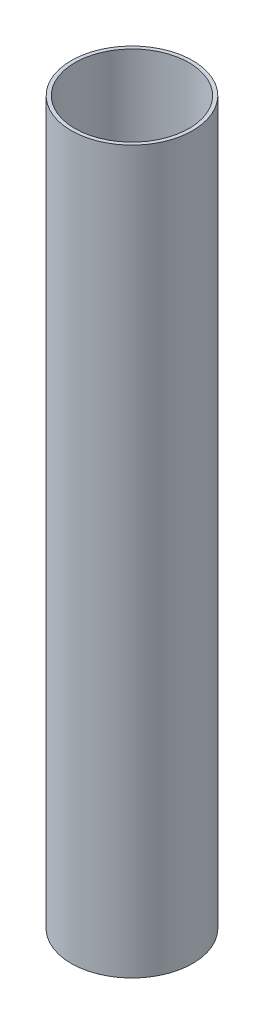
SolidWorks part; units mm, degrees
material "Alumina"
ref_plane "Front Plane" through (0, 0, 0) normal (0, 0, 1) x (1, 0, 0)
ref_plane "Top Plane" through (0, 0, 0) normal (0, 1, 0) x (1, 0, 0)
ref_plane "Right Plane" through (0, 0, 0) normal (1, 0, 0) x (0, 0, -1)
sketch "Sketch1" plane through (0, 0, 0) normal (0, 1, 0) x (1, 0, 0)
  circle A0 centre (0, 0) radius 25
  circle A1 centre (0, 0) radius 23.5
  dimension "D1" = 50
  dimension "D2" = 1.5
extrude "Boss-Extrude1" add sketch "Sketch1" along normal blind 297
